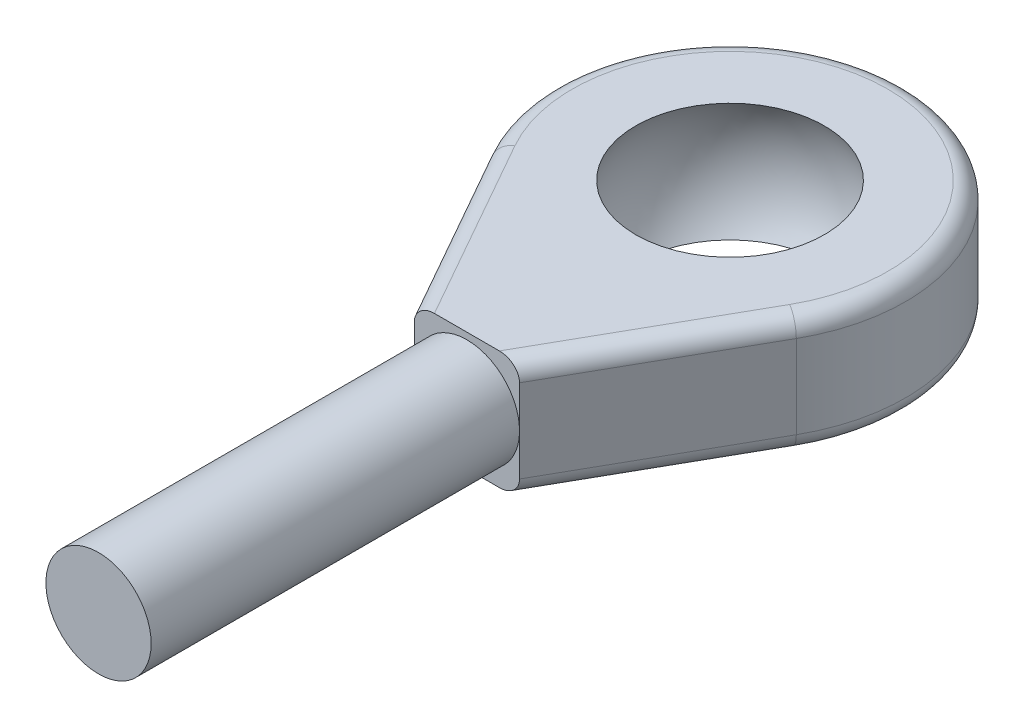
SolidWorks part; units mm, degrees
material "AISI 304"
ref_plane "前视基准面" through (0, 0, 0) normal (0, 0, 1) x (1, 0, 0)
ref_plane "上视基准面" through (0, 0, 0) normal (0, 1, 0) x (1, 0, 0)
ref_plane "右视基准面" through (0, 0, 0) normal (1, 0, 0) x (0, 0, -1)
sketch "草图1" plane through (0, 0, 0) normal (0, 1, 0) x (1, 0, 0)
  line L0 (-3, -15) -> (3, -15)
  line L1 (0, 10) -> (0, -15) construction
  line L2 (-3, -15) -> (-8.7025, -4.9262)
  line L3 (3, -15) -> (8.7025, -4.9262)
  arc A0 (8.7025, -4.9262) -> (-8.7025, -4.9262) centre (0, 0) ccw
  dimension "D1" = 20
  dimension "D2" = 15
  dimension "D3" = 6
extrude "凸台-拉伸1" add sketch "草图1" along normal mid plane 6.75
sketch "草图2" plane through (0, 0, 0) normal (1, 0, 0) x (0, 0, -1)
  line L0 (0, 6.35) -> (0, -6.35)
  arc A0 (0, -6.35) -> (0, 6.35) centre (0, 0) ccw
  dimension "D1" = 12.7
revolve "切除-旋转1" cut sketch "草图2" angle 360 about L0
fillet "圆角1" radius 1 6 edges at (5.8512, 3.375, 9.9631) (-5.8512, 3.375, 9.9631) (5.8512, -3.375, 9.9631) (-5.8512, -3.375, 9.9631) (0, 3.375, -10) (0, -3.375, -10)
sketch "草图3" plane through (0, 0, 15) normal (0, 0, 1) x (1, 0, 0)
  circle A0 centre (0, 0) radius 3
  dimension "D1" = 6
extrude "凸台-拉伸2" add sketch "草图3" along normal blind 21
cosmetic thread "装饰螺纹线1" parameters "D2"=4.917
ref_point "点1"
